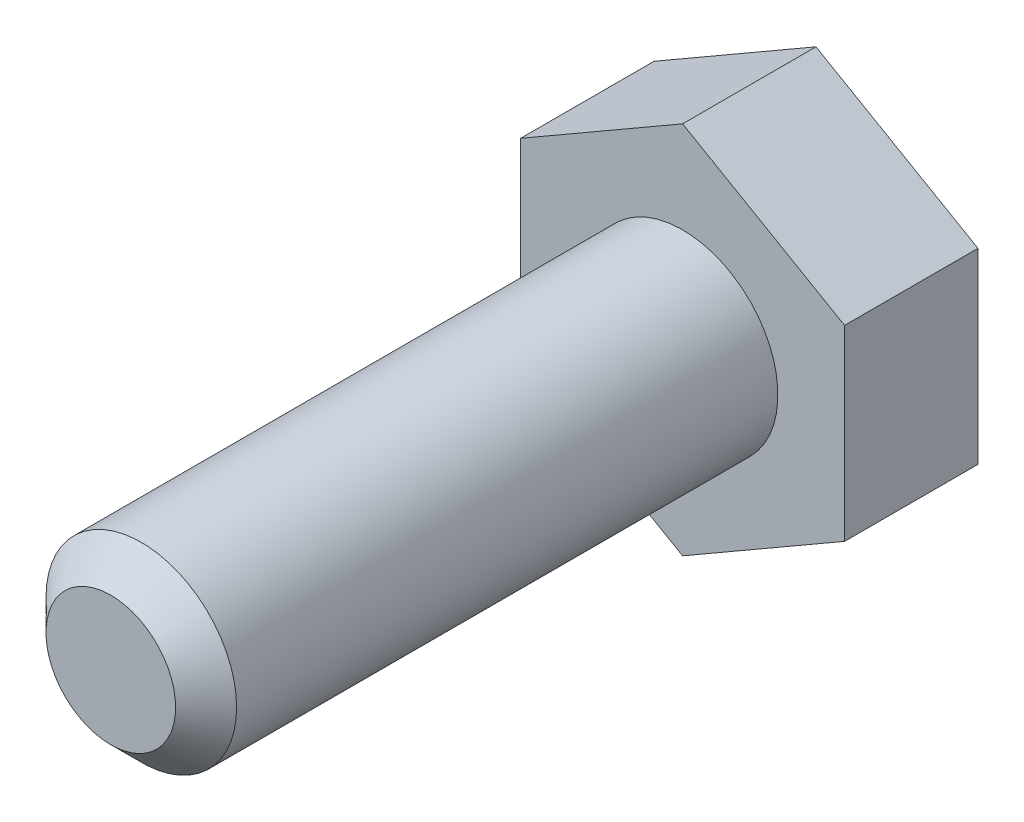
SolidWorks part; units mm, degrees
material "Сплав 3М ОСТ 1.92077-91"
ref_plane "Plane1" through (0, 0, 0) normal (0, 0, 1) x (1, 0, 0)
ref_plane "Plane2 - Gor" through (0, 0, 0) normal (0, 1, 0) x (1, 0, 0)
ref_plane "Plane3 - Ver" through (0, 0, 0) normal (1, 0, 0) x (0, 0, -1)
sketch "Sketch1" plane through (0, 0, 0) normal (0, 0, 1) x (1, 0, 0)
  circle A0 centre (0, 0) radius 5
  dimension "D1" = 10
extrude "Base-Extrude" add sketch "Sketch1" along normal blind 30
cosmetic thread "Cosmetic Thread2" parameters "D1"=30, "D2"=8.43
sketch "Sketch2" plane through (0, 0, 0) normal (0, 0, -1) x (-1, 0, 0)
  line L1 (0, 9.815) -> (-8.5, 4.9075)
  line L2 (-8.5, 4.9075) -> (-8.5, -4.9075)
  line L3 (-8.5, -4.9075) -> (0, -9.815)
  line L4 (0, -9.815) -> (8.5, -4.9075)
  line L5 (8.5, -4.9075) -> (8.5, 4.9075)
  line L6 (8.5, 4.9075) -> (0, 9.815)
  circle A0 centre (0, 0) radius 8.5 construction
  circle A1 centre (0, 0) radius 15 construction
  dimension "D1" = 17
  dimension "D2" = 30
extrude "Boss-Extrude2" add sketch "Sketch2" along normal blind 7
chamfer "Chamfer1" distance 1.6 angle 45 1 edges at (5, 0, 30)
